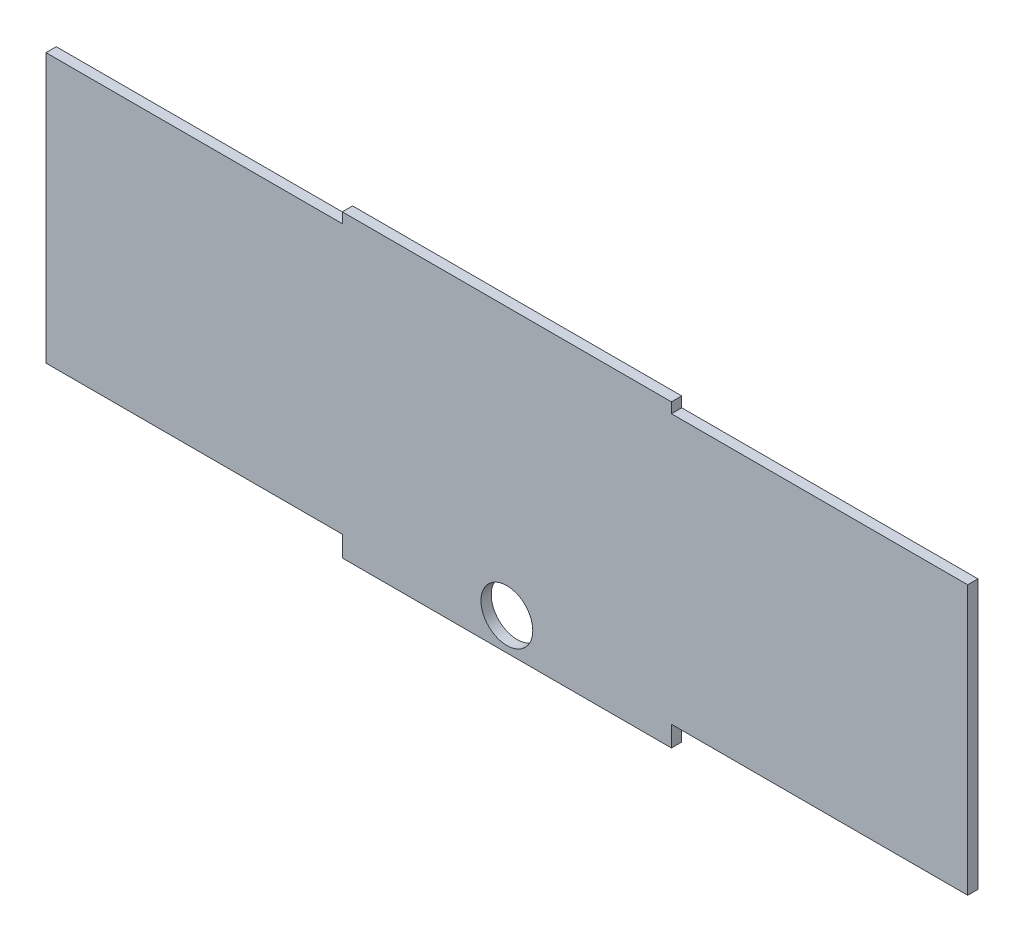
SolidWorks part; units mm, degrees
ref_plane "Front Plane" through (0, 0, 0) normal (0, 0, 1) x (1, 0, 0)
ref_plane "Top Plane" through (0, 0, 0) normal (0, 1, 0) x (1, 0, 0)
ref_plane "Right Plane" through (0, 0, 0) normal (1, 0, 0) x (0, 0, -1)
sketch "Sketch1" plane through (0, 0, 0) normal (0, 0, 1) x (1, 0, 0)
  line L0 (25.4, -20.75) -> (71.12, -20.75)
  line L1 (-71.12, 20.75) -> (-25.4, 20.75)
  line L2 (-71.12, 20.75) -> (-71.12, -20.75)
  line L3 (-71.12, -20.75) -> (-25.4, -20.75)
  line L4 (71.12, 20.75) -> (71.12, -20.75)
  line L6 (25.4, -20.75) -> (25.4, -23.925)
  line L8 (-25.4, -20.75) -> (-25.4, -23.925)
  line L14 (0, 0) -> (0, -32.5237) construction
  line L15 (-25.4, -23.925) -> (25.4, -23.925)
  line L16 (25.4, 20.75) -> (71.12, 20.75)
  line L17 (-25.4, 22.3375) -> (25.4, 22.3375)
  line L18 (-25.4, 22.3375) -> (-25.4, 20.75)
  line L20 (25.4, 22.3375) -> (25.4, 20.75)
  circle A0 centre (0, -18.925) radius 4
  point P12 (-71.12, 0)
  point P15 (0, 22.3375)
  dimension "D5" = 8
  dimension "D1" = 3.175
  dimension "D2" = 41.5
  dimension "D3" = 142.24
  dimension "D4" = 50.8
  dimension "D6" = 5
  dimension "D7" = 50.8
  dimension "D8" = 1.5875
extrude "Boss-Extrude1" add sketch "Sketch1" along normal mid plane 1.5875 contours L3 L8 L15 L6 L0 L4 L1 L2
